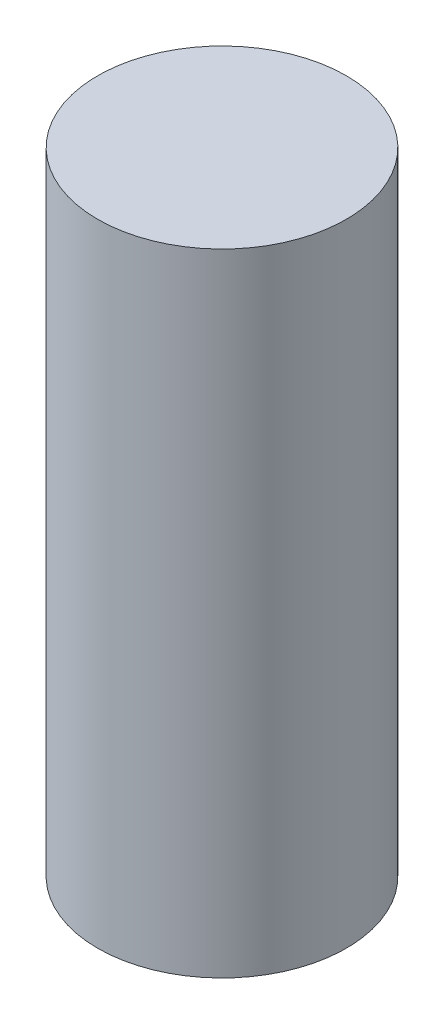
SolidWorks part; units mm, degrees
ref_plane "Front Plane" through (0, 0, 0) normal (0, 0, 1) x (1, 0, 0)
ref_plane "Top Plane" through (0, 0, 0) normal (0, 1, 0) x (1, 0, 0)
ref_plane "Right Plane" through (0, 0, 0) normal (1, 0, 0) x (0, 0, -1)
sketch "Sketch1" plane through (0, 0, 0) normal (0, 1, 0) x (1, 0, 0)
  circle A0 centre (0, 0) radius 6.35
  dimension "D1" = 12.7
extrude "Boss-Extrude1" add sketch "Sketch1" along normal blind 22.0751
sketch "Sketch2" plane through (0, 0, 0) normal (0, -1, 0) x (1, 0, 0)
  circle A0 centre (0, 0) radius 6.35
  dimension "D1" = 6.35
extrude "Boss-Extrude2" add sketch "Sketch2" along normal blind 10.16
hole_wizard "1/4-28 Tapped Hole1" positions "Sketch3" profile "Sketch4" tap size "1/4-28" standard "ANSI Inch"
sketch "Sketch3" plane through (0, -10.16, 0) normal (0, -1, 0) x (-1, 0, 0)
  point P0 (0, 0)
sketch "Sketch4" plane through (0, -10.16, 0) normal (1, 0, 0) x (0, 0, -1)
  line L0 (0, 0) -> (0, 17.1194)
  line L1 (0, 17.1194) -> (2.7051, 15.494)
  line L2 (2.7051, 15.494) -> (2.7051, 0)
  line L5 (2.7051, 0) -> (0, 0)
  line L10 (0, 17.1194) -> (-2.7051, 15.494) construction
  line L11 (0, -6.35) -> (0, 107.95) construction
  dimension "Tap Drill Dia." = 5.4102
  dimension "Tap Drill Depth" = 15.494
  dimension "Drill Angle" = 118
cosmetic thread "Hole Thread1" parameters "D1"=12.7, "D2"=6.35
sketch "Sketch5" plane through (0, 22.0751, 0) normal (0, 1, 0) x (1, 0, 0)
  circle A0 centre (0, 0) radius 6.35
  dimension "D1" = 12.7
extrude "Boss-Extrude3" add sketch "Sketch5" against normal blind 3.175
